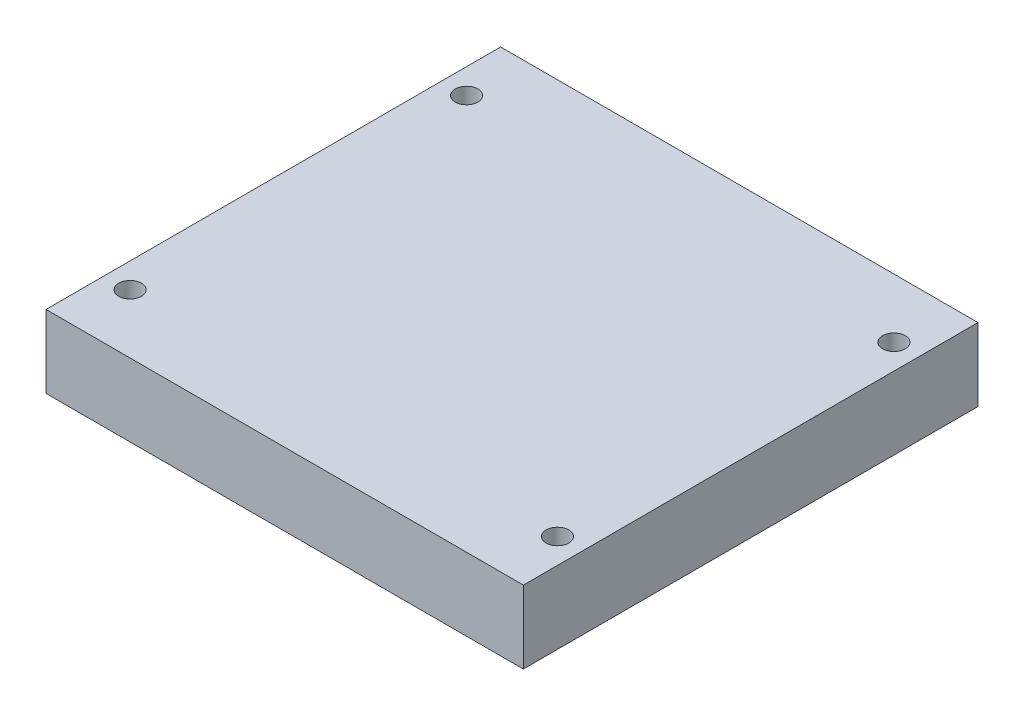
SolidWorks part; units mm, degrees
ref_plane "Front Plane" through (0, 0, 0) normal (0, 0, 1) x (1, 0, 0)
ref_plane "Top Plane" through (0, 0, 0) normal (0, 1, 0) x (1, 0, 0)
ref_plane "Right Plane" through (0, 0, 0) normal (1, 0, 0) x (0, 0, -1)
sketch "Sketch1" plane through (0, 0, 0) normal (0, 1, 0) x (1, 0, 0)
  line L0 (0, -110.8824) -> (0, 97.1468) construction
  line L1 (52.5, -50) -> (-52.5, -50)
  line L2 (52.5, -50) -> (52.5, 50)
  line L3 (52.5, 50) -> (-52.5, 50)
  line L4 (-52.5, -50) -> (-52.5, 50)
  line L5 (52.5, -50) -> (-52.5, 50) construction
  line L6 (52.5, 50) -> (-52.5, -50) construction
  line L7 (56.3085, 0) -> (-72.1235, 0) construction
  circle A1 centre (47, -37) radius 2.5
  circle A2 centre (47, 37) radius 2.5
  circle A3 centre (-47, 37) radius 2.5
  circle A4 centre (-47, -37) radius 2.5
  point P0 (0, 0)
  dimension "D3" = 5
  dimension "D1" = 105
  dimension "D2" = 100
  dimension "D4" = 47
  dimension "D5" = 37
extrude "Boss-Extrude2" add sketch "Sketch1" along normal blind 16 contours L4 L3 L2 L1 | A1 | A4 | A3 | A2
sketch "Sketch2" plane through (0, 0, 0) normal (0, 1, 0) x (1, 0, 0)
  circle A0 centre (0, 0) radius 45
  dimension "D1" = 90
extrude "Cut-Extrude1" cut sketch "Sketch2" along normal blind 12
chamfer "Chamfer1" distance 5 angle 45 1 edges at (0, 12, 45)
